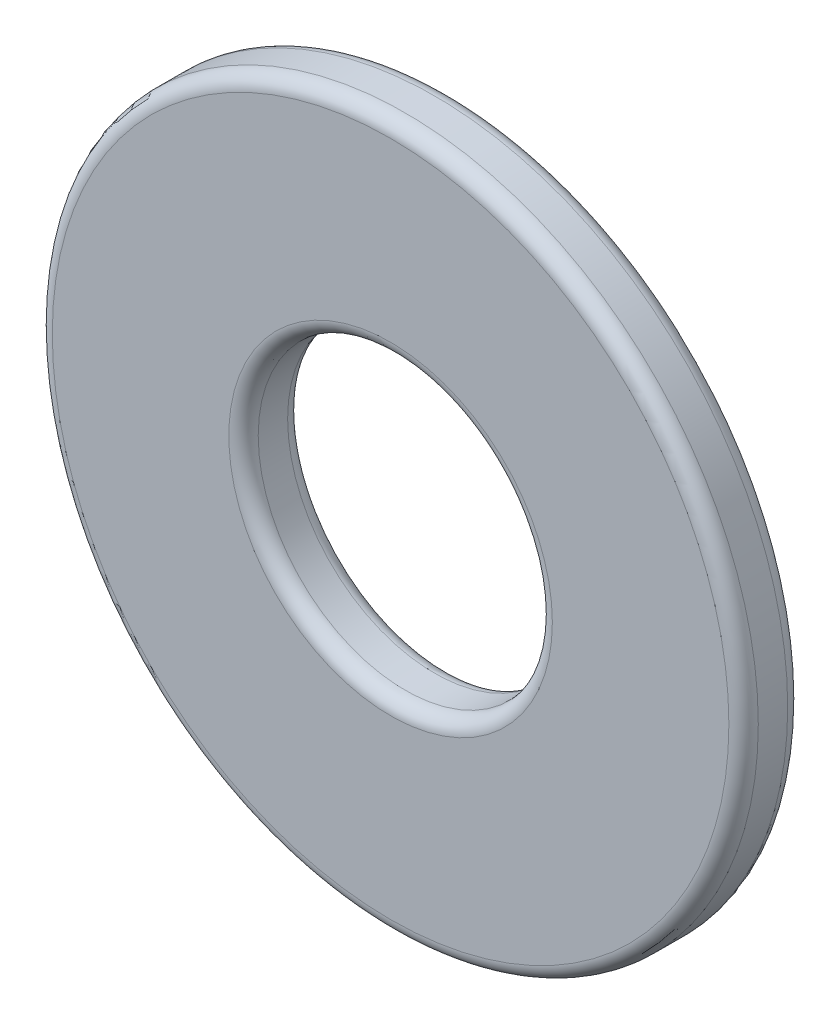
SolidWorks part; units mm, degrees
ref_plane "Front" through (0, 0, 0) normal (0, 0, 1) x (1, 0, 0)
ref_plane "Top" through (0, 0, 0) normal (0, 1, 0) x (1, 0, 0)
ref_plane "Right" through (0, 0, 0) normal (1, 0, 0) x (0, 0, -1)
sketch "Sketch1" plane through (0, 0, 0) normal (0, 0, 1) x (1, 0, 0)
  circle A0 centre (0, 0) radius 1.25
  circle A1 centre (0, 0) radius 3
  dimension "D1" = 2.5
  dimension "D2" = 6
extrude "Boss-Extrude1" add sketch "Sketch1" along normal blind 0.5
fillet "Fillet1" radius 0.125 4 edges at (3, 0, 0) (3, 0, 0.5) (1.25, 0, 0) (1.25, 0, 0.5)
